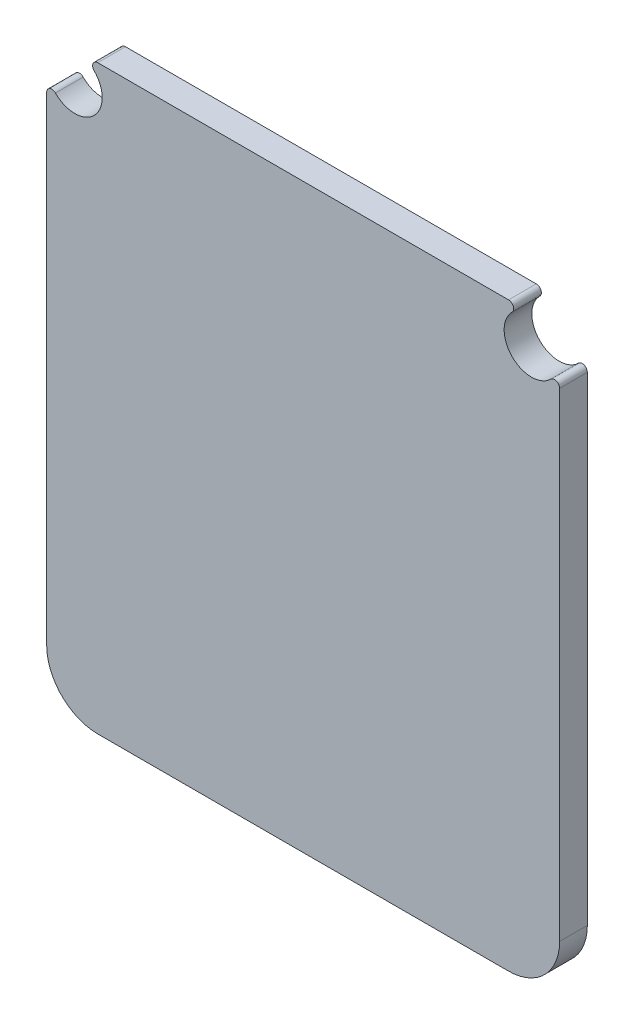
SolidWorks part; units mm, degrees
ref_plane "Front Plane" through (0, 0, 0) normal (0, 0, 1) x (1, 0, 0)
ref_plane "Top Plane" through (0, 0, 0) normal (0, 1, 0) x (1, 0, 0)
ref_plane "Right Plane" through (0, 0, 0) normal (1, 0, 0) x (0, 0, -1)
sketch "Sketch1" plane through (0, 0, 0) normal (0, 0, 1) x (1, 0, 0)
  line L0 (10, 29) -> (10, 57.013)
  line L1 (12.987, 60) -> (37.013, 60)
  line L2 (40, 57.013) -> (40, 29)
  line L3 (37, 26) -> (13, 26)
  arc A0 (10, 57.013) -> (10.5121, 57.2251) centre (10.3, 57.013) cw
  arc A1 (10.5121, 57.2251) -> (12.7749, 59.4879) centre (11.6463, 58.3537) ccw
  arc A2 (12.7749, 59.4879) -> (12.987, 60) centre (12.987, 59.7) cw
  arc A3 (37.013, 60) -> (37.2251, 59.4879) centre (37.013, 59.7) cw
  arc A4 (37.2251, 59.4879) -> (39.4879, 57.2251) centre (38.3551, 58.3551) ccw
  arc A5 (39.4879, 57.2251) -> (40, 57.013) centre (39.7, 57.013) cw
  arc A6 (40, 29) -> (37, 26) centre (37, 29) cw
  arc A7 (13, 26) -> (10, 29) centre (13, 29) cw
extrude "Board" add sketch "Sketch1" along normal blind 1.6194
